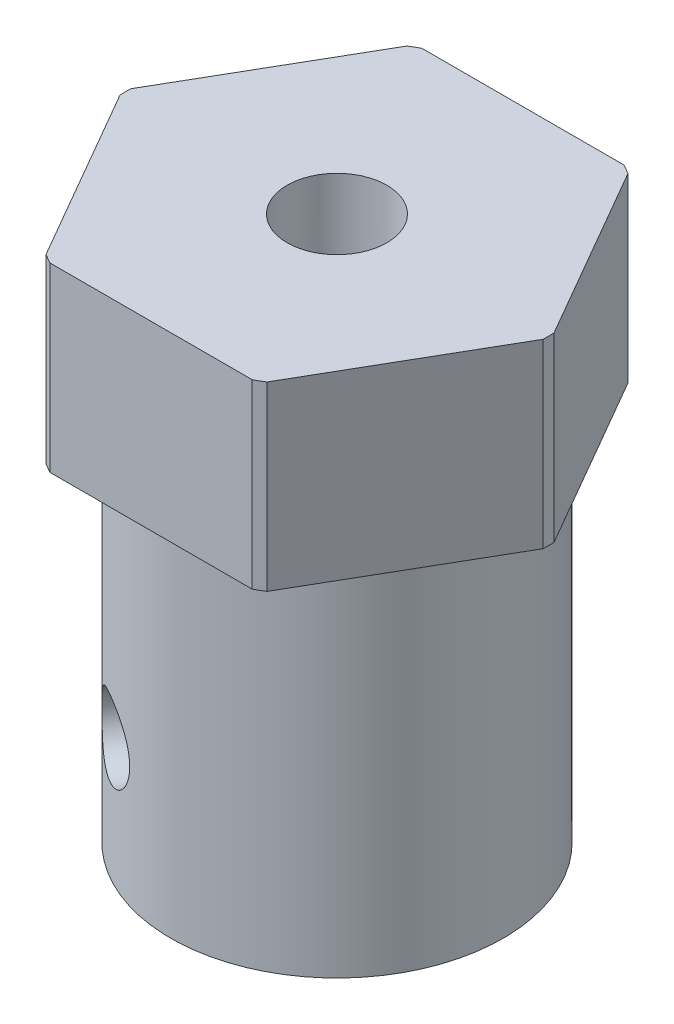
SolidWorks part; units mm, degrees
ref_plane "前视基准面" through (0, 0, 0) normal (0, 0, 1) x (1, 0, 0)
ref_plane "上视基准面" through (0, 0, 0) normal (0, 1, 0) x (1, 0, 0)
ref_plane "右视基准面" through (0, 0, 0) normal (1, 0, 0) x (0, 0, -1)
sketch "草图1" plane through (0, 0, 0) normal (0, 0, 1) x (1, 0, 0)
  line L0 (0, 0) -> (0, 18)
  line L1 (0, 18) -> (7, 18)
  line L2 (7, 18) -> (7, 12)
  line L3 (7, 12) -> (5.5, 12)
  line L4 (5.5, 12) -> (5.5, 0)
  line L5 (5.5, 0) -> (0, 0)
  dimension "D1" = 5.5
  dimension "D2" = 7
  dimension "D3" = 6
  dimension "D4" = 18
revolve "旋转1" add sketch "草图1" angle 360 about L0
sketch "草图2" plane through (0, 18, 0) normal (0, 1, 0) x (1, 0, 0)
  line L1 (7.1014, 0) -> (3.5507, 6.15)
  line L2 (3.5507, 6.15) -> (-3.5507, 6.15)
  line L3 (-3.5507, 6.15) -> (-7.1014, 0)
  line L4 (-7.1014, 0) -> (-3.5507, -6.15)
  line L5 (-3.5507, -6.15) -> (3.5507, -6.15)
  line L6 (3.5507, -6.15) -> (7.1014, 0)
  circle A0 centre (0, 0) radius 7.1014 construction
  dimension "D1" = 12.3
extrude "切除-拉伸1" cut sketch "草图2" against normal through all flip side to cut
hole_wizard "M4 螺纹孔1" positions "草图3" profile "草图4" tap size "M4" standard "ISO" end condition through all
sketch "草图3" plane through (0, 18, 0) normal (0, 1, 0) x (1, 0, 0)
  point P0 (0, 0)
cosmetic thread "孔螺蚊线1"
sketch "草图4" plane through (0, 18, 0) normal (1, 0, 0) x (0, 0, 1)
  line L0 (0, 0) -> (0, 18)
  line L1 (0, 18) -> (1.65, 18)
  line L2 (1.65, 18) -> (1.65, 0)
  line L5 (1.65, 0) -> (0, 0)
  line L11 (0, -6.35) -> (0, 107.95) construction
  dimension "通孔螺纹孔钻头直径" = 3.3
  dimension "通孔螺纹孔钻头深度" = 18
sketch "草图5" plane through (0, 0, 0) normal (0, -1, 0) x (1, 0, 0)
  circle A0 centre (0, 0) radius 3
  dimension "D1" = 6
extrude "切除-拉伸2" cut sketch "草图5" against normal blind 14 contours A0
ref_plane "基准面1" through (-2.75, 0, 4.7631) normal (0.5, 0, -0.866) x (-0.866, 0, -0.5)
hole_wizard "M3 螺纹孔1" positions "草图6" profile "草图7" tap size "M3" standard "ISO" end condition through all
sketch "草图6" plane through (-2.75, 0, 4.7631) normal (0.5, 0, -0.866) x (-0.866, 0, -0.5)
  point P0 (0, 4)
  dimension "D1" = 4
sketch "草图7" plane through (-2.75, 4, 4.7631) normal (0, 1, 0) x (0.866, 0, 0.5)
  line L0 (0, 0) -> (0, 14.3261)
  line L1 (0, 14.3261) -> (1.25, 14.3261)
  line L2 (1.25, 14.3261) -> (1.25, 0)
  line L5 (1.25, 0) -> (0, 0)
  line L11 (0, -6.35) -> (0, 107.95) construction
  dimension "通孔螺纹孔钻头直径" = 2.5
  dimension "通孔螺纹孔钻头深度" = 14.3261
cosmetic thread "孔螺蚊线2"
